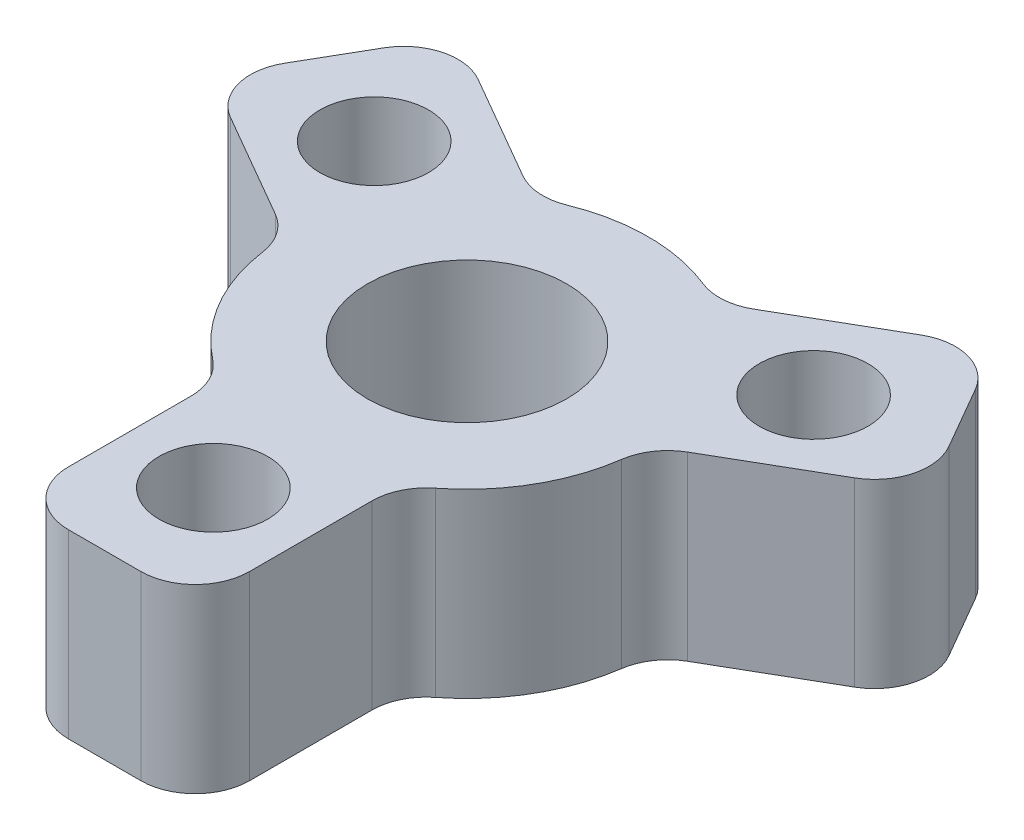
SolidWorks part; units mm, degrees
ref_plane "Front Plane" through (0, 0, 0) normal (0, 0, 1) x (1, 0, 0)
ref_plane "Top Plane" through (0, 0, 0) normal (0, 1, 0) x (1, 0, 0)
ref_plane "Right Plane" through (0, 0, 0) normal (1, 0, 0) x (0, 0, -1)
sketch "Sketch1" plane through (0, 0, 0) normal (0, 1, 0) x (1, 0, 0)
  circle A0 centre (0, 0) radius 5
  dimension "D1" = 10
extrude "Boss-Extrude1" add sketch "Sketch1" along normal blind 5
sketch "Sketch2" plane through (0, 0, 0) normal (0, 1, 0) x (1, 0, 0)
  line L0 (0, 0) -> (0, -5) construction
  line L2 (-2.5, -10) -> (2.5, -10)
  line L3 (-2.5, -10) -> (-2.5, 0)
  line L4 (-2.5, 0) -> (2.5, 0)
  line L5 (2.5, -10) -> (2.5, 0)
  line L6 (0, 0) -> (0, -10) construction
  line L7 (-2.5, -5) -> (2.5, -5) construction
  point P6 (0, 0)
  dimension "D1" = 5
  dimension "D2" = 10
extrude "Boss-Extrude2" add sketch "Sketch2" along normal up to surface (5 mm away) up to face at (0, 5, 5)
sketch "Sketch3" plane through (0, 5, 0) normal (0, 1, 0) x (1, 0, 0)
  line L0 (0, 0) -> (0, -10) construction
  line L1 (-2.5, -10) -> (2.5, -10) construction
  circle A0 centre (0, -7) radius 1.5
  dimension "D1" = 3
  dimension "D2" = 3
extrude "Cut-Extrude1" cut sketch "Sketch3" against normal through all
fillet "Fillet1" radius 1.5 4 edges at (-2.5, 2.5, 10) (2.5, 2.5, 10) (2.5, 2.5, 4.3301) (-2.5, 2.5, 4.3301)
pattern_circular "CirPattern1" count 3 over 360 about axis through (0, 0, 0) along (0, 1, 0) of "Boss-Extrude2", "Cut-Extrude1", "Fillet1"
sketch "Sketch4" plane through (0, 5, 0) normal (0, 1, 0) x (1, 0, 0)
  circle A0 centre (0, 0) radius 2.75
  dimension "D1" = 5.5
extrude "Cut-Extrude2" cut sketch "Sketch4" against normal through all
